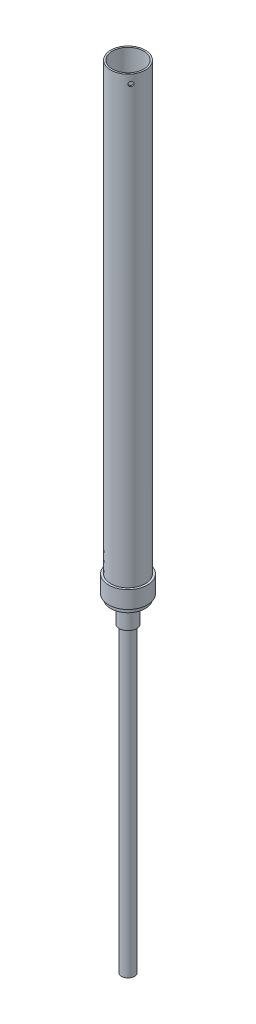
SolidWorks part; units mm, degrees
material "6061-T6 (SS)"
ref_plane "Front Plane" through (0, 0, 0) normal (0, 0, 1) x (1, 0, 0)
ref_plane "Top Plane" through (0, 0, 0) normal (0, 1, 0) x (1, 0, 0)
ref_plane "Right Plane" through (0, 0, 0) normal (1, 0, 0) x (0, 0, -1)
sketch "Sketch1" plane through (0, 0, 0) normal (0, 1, 0) x (1, 0, 0)
  circle A0 centre (0, 0) radius 25.4
  circle A1 centre (0, 0) radius 23.0188
  dimension "D1" = 50.8
  dimension "D2" = 46.0375
extrude "Boss-Extrude1" add sketch "Sketch1" along normal blind 679.45
sketch "Sketch2" plane through (0, 0, 0) normal (0, -1, 0) x (-1, 0, 0)
  circle A0 centre (0, 0) radius 25.4
  circle A1 centre (0, 0) radius 28.575
  dimension "D1" = 57.15
  dimension "D2" = 50.8
extrude "Boss-Extrude2" add sketch "Sketch2" against normal blind 25.4
sketch "Sketch3" plane through (0, 679.45, 0) normal (0, 1, 0) x (1, 0, 0)
  circle A0 centre (0, 0) radius 23.0187
  circle A1 centre (0, 0) radius 9.525
  dimension "D1" = 19.05
  dimension "D2" = 46.0375
extrude "Boss-Extrude3" [suppressed] add sketch "Sketch3" against normal blind 25.4
ref_plane "Plane1" through (15.5953, 0, -20.0486) normal (0.614, 0, -0.7893) x (-0.7893, 0, -0.614)
sketch "Sketch4" plane through (15.5953, 0, -20.0486) normal (0.614, 0, -0.7893) x (-0.7893, 0, -0.614)
  circle A0 centre (0, 55.5625) radius 1.8987
  circle A1 centre (0, 42.8625) radius 1.8986
  circle A2 centre (0, 30.1625) radius 1.8986
extrude "Cut-Extrude1" cut sketch "Sketch4" against normal through all
sketch "Sketch5" plane through (0, 0, 0) normal (0, -1, 0) x (1, 0, 0)
  circle A0 centre (0, 0) radius 25.4
  dimension "D1" = 50.8
extrude "Boss-Extrude4" add sketch "Sketch5" along normal blind 6.35
sketch "Sketch6" plane through (0, -6.35, 0) normal (0, -1, 0) x (1, 0, 0)
  circle A0 centre (0, 0) radius 12.7
  dimension "D1" = 25.4
extrude "Boss-Extrude5" add sketch "Sketch6" along normal blind 31.75
sketch "Sketch7" plane through (0, -38.1, 0) normal (0, -1, 0) x (1, 0, 0)
  circle A0 centre (0, 0) radius 9.525
  dimension "D1" = 19.05
extrude "Boss-Extrude6" add sketch "Sketch7" along normal blind 444.5
ref_plane "Plane2" through (20.0486, 0, 15.5953) normal (0.7893, 0, 0.614) x (0.614, 0, -0.7893)
hole_wizard "1/4 Clearance Hole1" positions "Sketch8" profile "Sketch9" hole size "1/4" standard "ANSI Inch"
sketch "Sketch8" plane through (20.0486, 0, 15.5953) normal (0.7893, 0, 0.614) x (0.614, 0, -0.7893)
  line L0 (0, 679.45) -> (0, 632.5891) construction
  line L1 (25.4, 679.45) -> (-25.4, 679.45) construction
  line L3 (23.0188, 679.45) -> (-23.0188, 679.45) construction
  point P0 (0, 666.75)
  dimension "D1" = 12.7
sketch "Sketch9" plane through (20.0486, 666.75, 15.5953) normal (0, 1, 0) x (0.614, 0, -0.7893)
  line L0 (0, 0) -> (0, 2.3813)
  line L1 (0, 2.3813) -> (3.3782, 2.3813)
  line L2 (3.3782, 2.3813) -> (3.3782, 0)
  line L5 (3.3782, 0) -> (0, 0)
  line L11 (0, -6.35) -> (0, 107.95) construction
  dimension "Thru Hole Dia." = 6.7564
  dimension "Thru Hole Depth" = 2.3813
